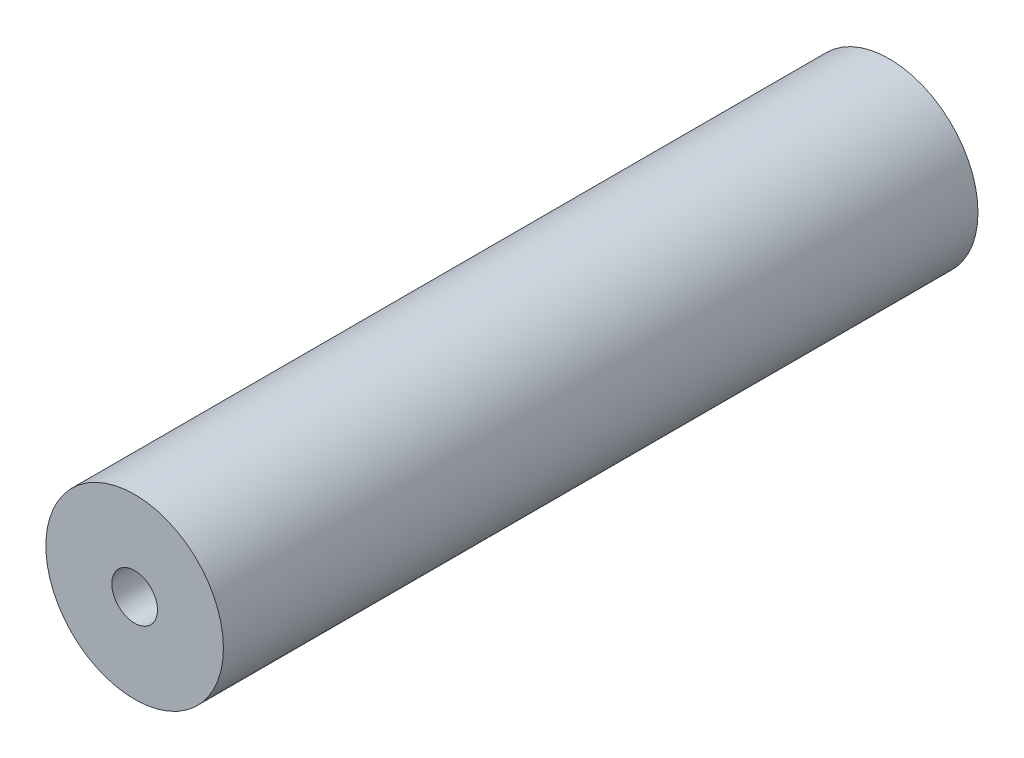
SolidWorks part; units mm, degrees
material "Alum 6061 (Default)"
ref_plane "Front Plane" through (0, 0, 0) normal (0, 0, 1) x (1, 0, 0)
ref_plane "Top Plane" through (0, 0, 0) normal (0, 1, 0) x (1, 0, 0)
ref_plane "Right Plane" through (0, 0, 0) normal (1, 0, 0) x (0, 0, -1)
sketch "Sketch1" plane through (0, 0, 0) normal (0, 0, 1) x (1, 0, 0)
  circle A0 centre (0, 0) radius 12.7
  dimension "Diameter" = 25.4
extrude "Extrude1" add sketch "Sketch1" along normal mid plane 107.95
hole_wizard "5/16-18 Tapped Hole1" positions "Sketch2" profile "Sketch3" tap size "5/16-18" standard "ANSI Inch"
sketch "Sketch2" plane through (0, 0, 53.975) normal (0, 0, 1) x (1, 0, 0)
  point P0 (0, 0)
sketch "Sketch3" plane through (0, 0, 53.975) normal (1, 0, 0) x (0, -1, 0)
  line L0 (0, 0) -> (0, 22.2811)
  line L1 (0, 22.2811) -> (3.2639, 20.32)
  line L2 (3.2639, 20.32) -> (3.2639, 0)
  line L5 (3.2639, 0) -> (0, 0)
  line L10 (0, 22.2811) -> (-3.2639, 20.32) construction
  line L11 (0, -6.35) -> (0, 107.95) construction
  dimension "Tap Drill Dia." = 6.5278
  dimension "Tap Drill Depth" = 20.32
  dimension "Drill Angle" = 118
cosmetic thread "Hole Thread1" parameters "D1"=16.002, "D2"=7.9375
